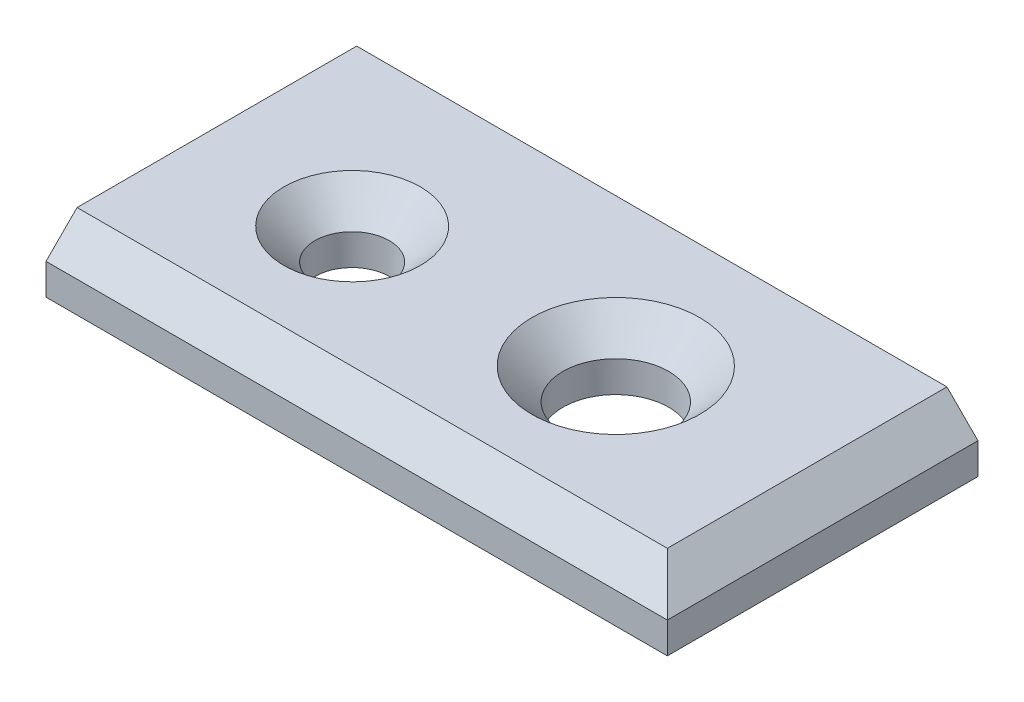
SolidWorks part; units mm, degrees
other "Defeature"
ref_plane "XY-Vorderansicht" through (0, 0, 0) normal (0, 0, 1) x (1, 0, 0)
ref_plane "XZ-Draufsicht" through (0, 0, 0) normal (0, 1, 0) x (1, 0, 0)
ref_plane "YZ-Seitenansicht" through (0, 0, 0) normal (1, 0, 0) x (0, 0, -1)
sketch "Skizze1" plane through (0, 0, 0) normal (0, 1, 0) x (1, 0, 0)
  line L1 (0, 0) -> (100, 0)
  line L2 (0, 0) -> (0, 50)
  line L3 (0, 50) -> (100, 50)
  line L4 (100, 0) -> (100, 50)
  dimension "D1" = 100
  dimension "D2" = 50
extrude "Aufsatz-Linear austragen1" add sketch "Skizze1" along normal blind 10
sketch "Skizze2" plane through (0, 10, 0) normal (0, 1, 0) x (1, 0, 0)
  circle A0 centre (24.7348, 24.5365) radius 5.979
extrude "Schnitt-Linear austragen1" cut sketch "Skizze2" against normal through all
chamfer "Fase1" distance 5 angle 45 3 edges at (100, 10, -25) (50, 10, 0) (24.7348, 10, -18.5575)
sketch "Skizze3" plane through (0, 10, 0) normal (0, 1, 0) x (1, 0, 0)
  circle A0 centre (65.4402, 26.2668) radius 8.5048
extrude "Schnitt mit extra Fase" cut sketch "Skizze3" against normal through all
chamfer "Fase2" distance 5 angle 45 1 edges at (65.4402, 10, -17.762)
